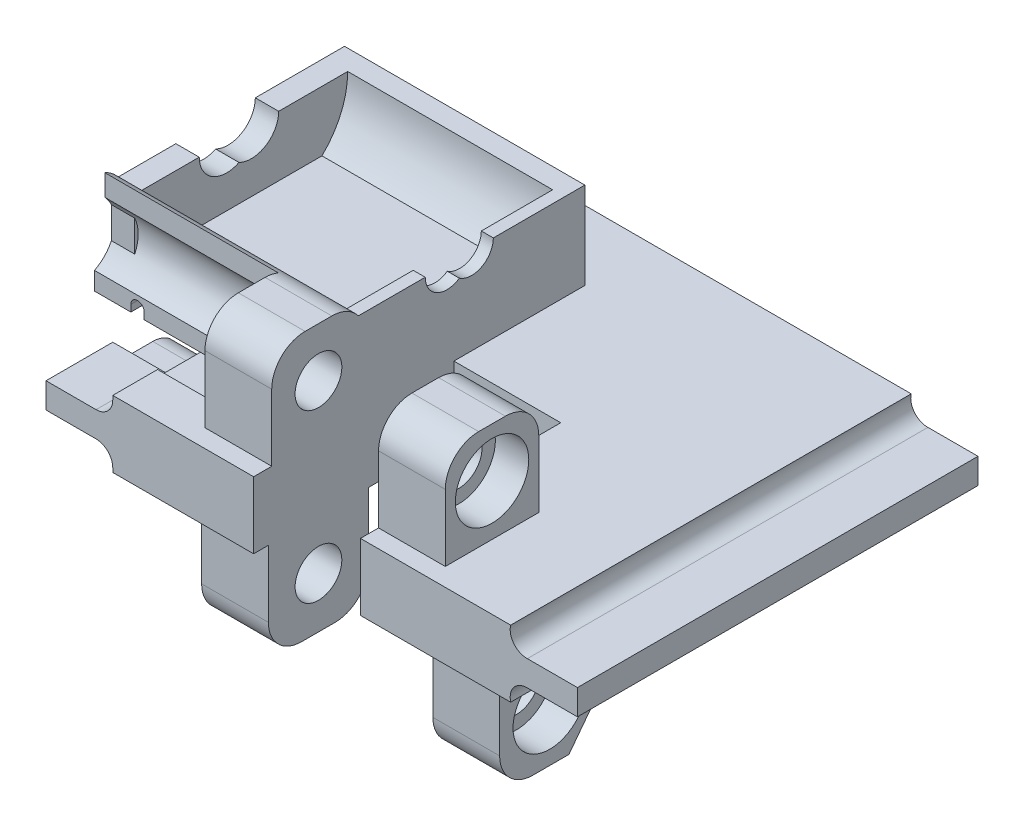
SolidWorks part; units mm, degrees
material "ABS"
ref_plane "정면" through (0, 0, 0) normal (0, 0, 1) x (1, 0, 0)
ref_plane "윗면" through (0, 0, 0) normal (0, 1, 0) x (1, 0, 0)
ref_plane "우측면" through (0, 0, 0) normal (1, 0, 0) x (0, 0, -1)
sketch "스케치1" plane through (0, 0, 0) normal (0, 0, 1) x (1, 0, 0)
  line L0 (0, 0) -> (0, 10)
  line L1 (29.8, 10) -> (-29.8, 10)
  line L2 (-32.3, 6.9) -> (-39.8, 6.9)
  line L3 (-39.8, 6.9) -> (-39.8, 3.1)
  line L4 (-39.8, 3.1) -> (-32.3, 3.1)
  line L5 (-29.8, 0) -> (29.8, 0)
  line L6 (39.8, 3.1) -> (32.3, 3.1)
  line L7 (39.8, 6.9) -> (39.8, 3.1)
  line L8 (32.3, 6.9) -> (39.8, 6.9)
  line L9 (-29.8, 10) -> (-29.8, 9.4)
  line L10 (-29.8, 0.6) -> (-29.8, 0)
  arc A2 (32.3, 3.1) -> (29.8, 0) centre (32.2267, 0.6011) ccw
  arc A3 (29.8, 10) -> (32.3, 6.9) centre (32.2267, 9.3989) ccw
  arc A5 (-32.3, 3.1) -> (-29.8, 0.6) centre (-32.3, 0.6) cw
  arc A6 (-29.8, 9.4) -> (-32.3, 6.9) centre (-32.3, 9.4) cw
  point P13 (0, 5)
  point P14 (-39.8, 5)
  dimension "D5" = 2.5
  dimension "D6" = 2.5
  dimension "D1" = 39.8
  dimension "D2" = 29.8
  dimension "D3" = 10
  dimension "D4" = 29.8
  dimension "D7" = 3.8
extrude "보스-돌출1" add sketch "스케치1" along normal blind 60
sketch "스케치2" plane through (-39.8, 0, 0) normal (-1, 0, 0) x (0, 0, 1)
  line L1 (44, 4) -> (50, 4)
  line L2 (50, 4) -> (50, 8)
  line L3 (16, 4) -> (10, 4)
  line L4 (50, 8) -> (10, 8)
  line L5 (30, 8) -> (30, 0)
  line L6 (20, 0) -> (40, 0)
  line L7 (60, 6.9) -> (60, 3.1) construction
  line L8 (10, 4) -> (10, 8)
  line L9 (60, 0) -> (0, 0) construction
  arc A0 (40, 0) -> (44, 4) centre (44, 0) cw
  arc A1 (20, 0) -> (16, 4) centre (16, 0) ccw
  line M12 (0, 3.1) -> (60, 3.1)
  line M14 (60, 6.9) -> (0, 6.9)
  dimension "D4" = 4
  dimension "D1" = 4
  dimension "D2" = 4
  dimension "D3" = 10
  dimension "D5" = 20
  dimension "D6" = 10
extrude "컷-돌출1" cut sketch "스케치2" against normal blind 17.3 contours A1 L5 L8 L3 M12 M14 | L6 A0 L5 M12 | A0 L1 L2 L5 M12 M14
sketch "Sketch1" plane through (0, 10, 0) normal (0, 1, 0) x (1, 0, 0)
  line L0 (29.8, -60) -> (-29.8, -60) construction
  line L1 (7.3, -60) -> (-8.7, -60)
  line L2 (7.3, -60) -> (7.3, -30)
  line L3 (7.3, -30) -> (-8.7, -30)
  line L4 (-8.7, -60) -> (-8.7, -30)
  line L5 (29.8, -60) -> (29.8, 0) construction
  dimension "D1" = 22.5
  dimension "D2" = 30
  dimension "D3" = 16
extrude "Cut-Extrude1" cut sketch "Sketch1" against normal blind 10
sketch "Sketch2" plane through (7.3, 0, 0) normal (-1, 0, 0) x (0, 0, 1)
  line L0 (60, 10) -> (30, 10) construction
  line L6 (57.29, 10) -> (43.29, 10)
  line L7 (57.29, 10) -> (57.29, 20)
  line L8 (52.29, 25) -> (48.29, 25)
  line L9 (43.29, 10) -> (43.29, 20)
  circle A0 centre (50.29, 17.61) radius 3.5
  arc A3 (48.29, 25) -> (43.29, 20) centre (48.29, 20) ccw
  arc A4 (57.29, 20) -> (52.29, 25) centre (52.29, 20) ccw
  point P1 (50.29, 25)
  point P11 (43.29, 25)
  point P15 (57.29, 25)
  dimension "D1" = 7
  dimension "D2" = 14
  dimension "D6" = 5
  dimension "D3" = 7.61
  dimension "D4" = 9.71
  dimension "D5" = 15
extrude "Boss-Extrude1" add sketch "Sketch2" against normal blind 10
sketch "Sketch4" plane through (17.3, 0, 0) normal (1, 0, 0) x (0, 0, -1)
  circle A0 centre (-50.29, 17.61) radius 5.5
  dimension "D1" = 11
extrude "Cut-Extrude4" cut sketch "Sketch4" against normal blind 5
ref_plane "Plane1" through (-0.7, 0, 0) normal (-1, 0, 0) x (0, 0, 1)
mirror "Mirror1" about plane through (-0.7, 0, 0) normal (-1, 0, 0) of "Cut-Extrude4", "Boss-Extrude1"
sketch "Sketch5" plane through (-8.7, 0, 0) normal (1, 0, 0) x (0, 0, -1)
  line L0 (-30, 0) -> (-60, 0) construction
  line L1 (-60, 0) -> (-60, 10) construction
  line L3 (-57.79, 0) -> (-42.79, 0)
  line L4 (-57.79, 0) -> (-57.79, -10)
  line L5 (-52.79, -15) -> (-47.79, -15)
  line L6 (-42.79, 0) -> (-42.79, -10)
  circle A0 centre (-50.29, -7.39) radius 3.5
  arc A1 (-47.79, -15) -> (-42.79, -10) centre (-47.79, -10) ccw
  arc A2 (-57.79, -10) -> (-52.79, -15) centre (-52.79, -10) ccw
  point P11 (-50.29, -15)
  point P14 (-42.79, -15)
  point P17 (-57.79, -15)
  dimension "D1" = 7
  dimension "D6" = 5
  dimension "D2" = 7.39
  dimension "D3" = 9.71
  dimension "D4" = 15
  dimension "D5" = 15
extrude "Boss-Extrude2" add sketch "Sketch5" against normal blind 10
sketch "Sketch6" plane through (-18.7, 0, 0) normal (-1, 0, 0) x (0, 0, 1)
  circle A0 centre (50.29, -7.39) radius 5.5
  dimension "D1" = 11
extrude "Cut-Extrude5" cut sketch "Sketch6" against normal blind 5
ref_plane "Plane2" through (3.62, 0, 0) normal (1, 0, 0) x (0, 0, -1)
mirror "Mirror2" about plane through (3.62, 0, 0) normal (1, 0, 0) of "Cut-Extrude5", "Boss-Extrude2"
sketch "Sketch7" plane through (-8.7, 0, 0) normal (1, 0, 0) x (0, 0, -1)
  line L0 (-30, 0) -> (-30, 10) construction
  line L1 (-30, 10) -> (-43.29, 10) construction
  line L2 (-40.0582, 14) -> (-17.2618, 14)
  line L4 (-39.4431, 32.6025) -> (-17.8769, 32.6025)
  line L8 (-46.1326, 23.0254) -> (-10.3854, 23.0254)
  line L9 (-46.1326, 36.0509) -> (-10.3854, 36.0509)
  line L10 (-46.1326, 36.0509) -> (-46.1326, 10)
  line L11 (-46.1326, 10) -> (-10.3854, 10)
  line L12 (-10.3854, 36.0509) -> (-10.3854, 10)
  arc A1 (-17.2618, 14) -> (-17.8769, 32.6025) centre (-25.91, 23.0254) ccw
  arc A2 (-39.4431, 32.6025) -> (-40.0582, 14) centre (-31.41, 23.0254) ccw
  point P7 (-45.1928, 23.0254)
  point P11 (0, 0)
  dimension "D2" = 12.5
  dimension "D6" = 12.5
  dimension "D1" = 4.09
  dimension "D3" = 4
  dimension "D4" = 5.5
  dimension "D5" = 22.6025
extrude "Boss-Extrude4" add sketch "Sketch7" against normal blind 36
sketch "Sketch8" plane through (0, 23.0254, 0) normal (0, 1, 0) x (1, 0, 0)
  line L1 (-8.7, -13.41) -> (-10.5, -13.41)
  line L2 (-8.7, -13.41) -> (-8.7, -45.828)
  line L3 (-8.7, -45.828) -> (-10.5, -45.828)
  line L4 (-10.5, -13.41) -> (-10.5, -45.828)
  line L6 (-44.7, -13.41) -> (-41.2, -13.41)
  line L7 (-44.7, -13.41) -> (-44.7, -45.3107)
  line L8 (-44.7, -45.3107) -> (-41.2, -45.3107)
  line L9 (-41.2, -13.41) -> (-41.2, -45.3107)
  dimension "D1" = 1.8
  dimension "D2" = 3.5
extrude "Boss-Extrude5" add sketch "Sketch8" against normal blind 10
sketch "Sketch9" plane through (-8.7, 0, 0) normal (1, 0, 0) x (0, 0, -1)
  line L0 (-44.3092, 23.0254) -> (-10.3854, 23.0254) construction
  line L1 (-44.3092, 23.0254) -> (-10.3854, 23.0254) construction
  circle A0 centre (-27.3473, 23.0254) radius 3.25
  circle A1 centre (-31.0473, 23.0254) radius 3.25
  line M2 (-10.3854, 23.0254) -> (-44.3092, 23.0254)
  dimension "D1" = 6.5
  dimension "D2" = 6.5
  dimension "D3" = 3.7
extrude "Cut-Extrude6" cut sketch "Sketch9" against normal blind 10 contours A1 A0 M2 | A1 A0 M2
sketch "Sketch10" plane through (-44.7, 0, 0) normal (-1, 0, 0) x (0, 0, 1)
  line L0 (45.3107, 23.0254) -> (10.3854, 23.0254) construction
  line L1 (45.3107, 23.0254) -> (10.3854, 23.0254) construction
  circle A0 centre (27.8481, 23.0254) radius 4.1
  circle A1 centre (31.5481, 23.0254) radius 4.1
  line M10 (45.3107, 23.0254) -> (10.3854, 23.0254)
  dimension "D1" = 8.2
  dimension "D2" = 8.2
  dimension "D3" = 3.7
extrude "Cut-Extrude7" cut sketch "Sketch10" against normal blind 10 contours A1 A0 M10 | A1 A0 M10 | A0 A1 M10
sketch "Sketch12" plane through (25.94, 0, 0) normal (1, 0, 0) x (0, 0, -1)
  line L0 (-42.79, -8.9362) -> (-47.4024, -14.985)
  line L1 (-42.79, -10) -> (-42.79, 0) construction
  line L2 (-47.4024, -14.985) -> (-43.1675, -15.5436)
  line L3 (-43.1675, -15.5436) -> (-40.8892, -10)
  line L4 (-40.8892, -10) -> (-42.79, -8.9362)
  arc A0 (-47.79, -15) -> (-42.79, -10) centre (-47.79, -10) ccw construction
extrude "Cut-Extrude9" cut sketch "Sketch12" against normal blind 10
sketch "Sketch13" plane through (0, 0, 43.29) normal (0, 0, 1) x (1, 0, 0)
  line L0 (-29.8, 10) -> (-23.7804, 10)
  line L1 (-29.8, 10) -> (-18.7, 10) construction
  line L2 (-23.7804, 10) -> (-23.7804, 11.1029)
  line L3 (-21.7804, 11.1029) -> (-21.7804, 9)
  line L4 (-21.7804, 9) -> (-30.476, 9)
  line L5 (-30.476, 9) -> (-29.8, 10)
  arc A0 (-23.7804, 11.1029) -> (-21.7804, 11.1029) centre (-22.7804, 11.1029) cw
  dimension "D2" = 1
  dimension "D1" = 1
extrude "Cut-Extrude10" cut sketch "Sketch13" against normal blind 35 and the other way blind 10
sketch "Sketch11" plane through (0, 0, 43.29) normal (0, 0, 1) x (1, 0, 0)
  line L0 (-39.25, 10) -> (-39.25, 11)
  line L2 (-37.25, 11) -> (-37.25, 10)
  line L3 (-37.25, 10) -> (-39.25, 10)
  arc A0 (-39.25, 11) -> (-37.25, 11) centre (-38.25, 11) cw
  dimension "D1" = 1
  dimension "D2" = 1
  dimension "D3" = 2
extrude "Cut-Extrude8" cut sketch "Sketch11" against normal through all and the other way blind 24
sketch "Sketch14" plane through (-18.7, 0, 0) normal (-1, 0, 0) x (0, 0, 1)
  line L1 (47.8417, 12.685) -> (47.8417, 10)
  line L2 (43.29, 10) -> (57.29, 10) construction
  line L3 (47.8417, 10) -> (43.29, 10)
  line L4 (43.29, 10) -> (43.29, 20)
  circle A0 centre (50.29, 17.61) radius 5.5 construction
  arc A1 (46.2859, 21.3806) -> (47.8417, 12.685) centre (50.29, 17.61) ccw
sketch "Sketch17" plane through (-18.7, 0, 0) normal (-1, 0, 0) x (0, 0, 1)
  line L0 (43.29, 10) -> (47.8417, 10)
  line L1 (47.8417, 10) -> (47.8417, 12.685)
  line L2 (46.2859, 21.3806) -> (46.2859, 24.5808)
  line L3 (43.29, 20) -> (43.29, 10)
  arc A0 (47.8417, 12.685) -> (46.2859, 21.3806) centre (50.29, 17.61) cw
  arc A1 (48.29, 25) -> (43.29, 20) centre (48.29, 20) ccw construction
  arc A2 (46.2859, 24.5808) -> (43.29, 20) centre (48.29, 20) ccw
  arc A3 (46.2859, 21.3806) -> (47.8417, 12.685) centre (50.29, 17.61) ccw construction
extrude "Boss-Extrude8" add sketch "Sketch17" along normal up to surface (26 mm away) up to face at (-44.7, 17.1326, 31.8963)
sketch "Sketch16" plane through (-10.5, 0, 0) normal (-1, 0, 0) x (0, 0, 1)
  line L0 (39.21, 14) -> (40.0582, 14)
  line L1 (40.0582, 14) -> (17.2618, 14) construction
  line L2 (34.2973, 23.0254) -> (44.3092, 23.0254) construction
  line L3 (43.91, 23.0254) -> (41.1378, 23.0254)
  line L4 (41.1378, 23.0254) -> (39.21, 14)
  arc A0 (40.0582, 14) -> (43.91, 23.0254) centre (31.41, 23.0254) ccw
  arc A1 (40.0582, 14) -> (43.29, 19.1376) centre (31.41, 23.0254) ccw construction
extrude "Cut-Extrude12" cut sketch "Sketch16" along normal up to surface (30.7 mm away) up to face at (-41.2, 19.4189, 32.2066)
sketch "Sketch18" plane through (0, 0, 43.29) normal (0, 0, -1) x (-1, 0, 0)
  line L6 (21.7804, 11.1029) -> (21.7804, 10)
  line L7 (21.7804, 10) -> (23.7804, 10)
  line L8 (23.7804, 10) -> (23.7804, 11.1029)
  line L9 (21.7804, 11.1029) -> (21.7804, 10)
  line L10 (21.7804, 10) -> (23.7804, 10)
  line L11 (23.7804, 10) -> (23.7804, 11.1029)
  arc A2 (23.7804, 11.1029) -> (21.7804, 11.1029) centre (22.7804, 11.1029) ccw
  arc A3 (23.7804, 11.1029) -> (21.7804, 11.1029) centre (22.7804, 11.1029) ccw
  dimension "D1" = 0
extrude "Cut-Extrude13" cut sketch "Sketch18" against normal up to surface (4.5517 mm away) up to face at (-29.7161, 11.074, 47.8417)
sketch "Sketch19" plane through (0, 0, 43.29) normal (0, 0, -1) x (-1, 0, 0)
  line L6 (37.25, 11) -> (37.25, 10)
  line L7 (37.25, 10) -> (39.25, 10)
  line L8 (39.25, 10) -> (39.25, 11)
  line L9 (37.25, 11) -> (37.25, 10)
  line L10 (37.25, 10) -> (39.25, 10)
  line L11 (39.25, 10) -> (39.25, 11)
  arc A2 (39.25, 11) -> (37.25, 11) centre (38.25, 11) ccw
  arc A3 (39.25, 11) -> (37.25, 11) centre (38.25, 11) ccw
  dimension "D1" = 0
extrude "Cut-Extrude14" cut sketch "Sketch19" against normal blind 14
